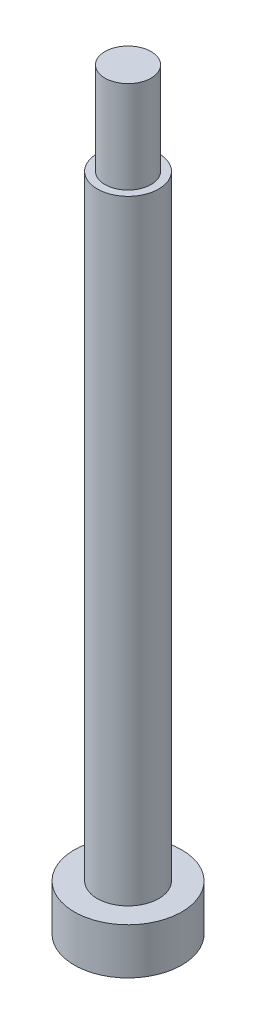
SolidWorks part; units mm, degrees
material "1060 合金"
ref_plane "前视基准面" through (0, 0, 0) normal (0, 0, 1) x (1, 0, 0)
ref_plane "上视基准面" through (0, 0, 0) normal (0, 1, 0) x (1, 0, 0)
ref_plane "右视基准面" through (0, 0, 0) normal (1, 0, 0) x (0, 0, -1)
sketch "草图1" plane through (0, 0, 0) normal (0, 1, 0) x (1, 0, 0)
  circle A0 centre (0, 0) radius 2
  dimension "D1" = 4
extrude "凸台-拉伸1" add sketch "草图1" along normal blind 40
sketch "草图2" plane through (0, 40, 0) normal (0, 1, 0) x (1, 0, 0)
  circle A0 centre (0, 0) radius 1.5
  dimension "D1" = 3
extrude "凸台-拉伸2" add sketch "草图2" along normal blind 6
cosmetic thread "装饰螺纹线1" parameters "D2"=2.459
sketch "草图3" plane through (0, 0, 0) normal (0, -1, 0) x (1, 0, 0)
  circle A0 centre (0, 0) radius 3.5
  dimension "D1" = 7
extrude "凸台-拉伸3" add sketch "草图3" along normal blind 3
